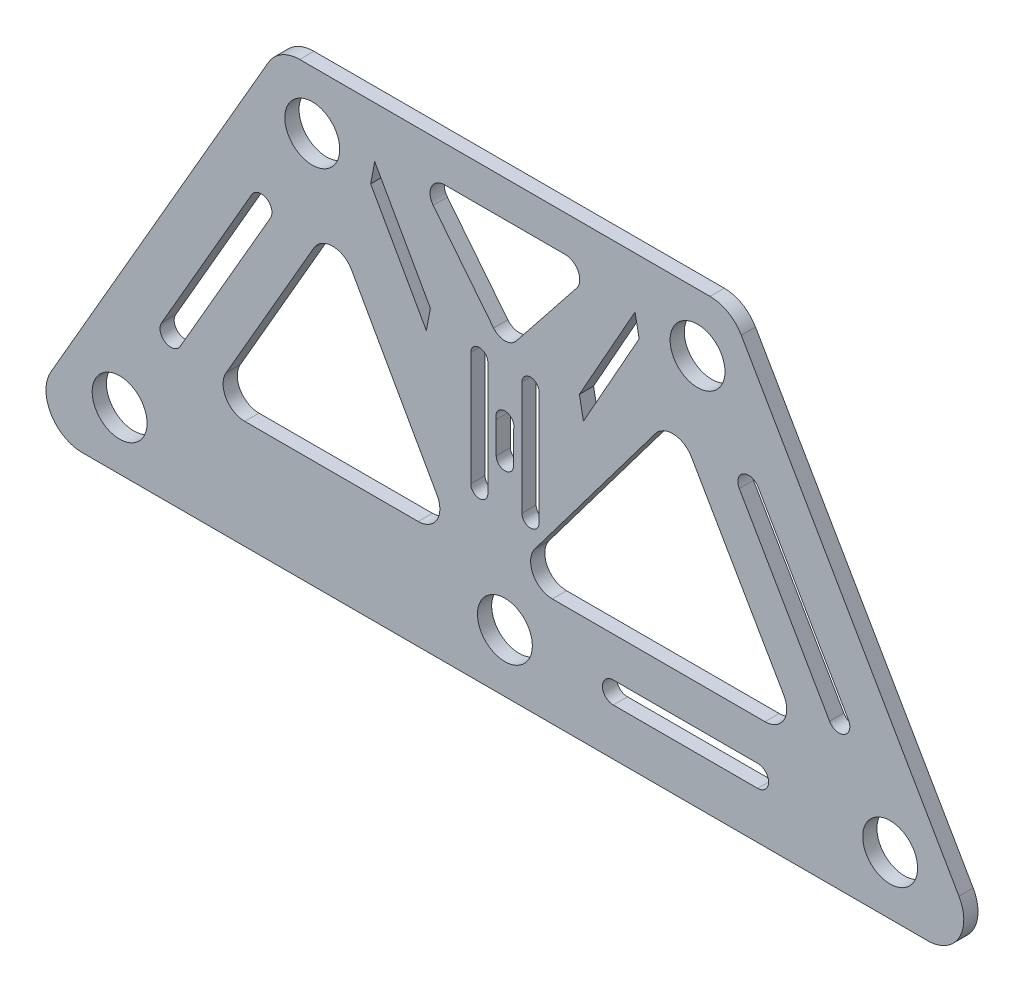
SolidWorks part; units mm, degrees
material "Acrylic (Medium-high impact)"
ref_plane "Front Plane" through (0, 0, 0) normal (0, 0, 1) x (1, 0, 0)
ref_plane "Top Plane" through (0, 0, 0) normal (0, 1, 0) x (1, 0, 0)
ref_plane "Right Plane" through (0, 0, 0) normal (1, 0, 0) x (0, 0, -1)
sketch "Sketch1" plane through (0, 0, 0) normal (0, 0, 1) x (1, 0, 0)
  line L0 (135.4667, 0) -> (-135.4667, 0) construction
  line L1 (0, 0) -> (135.4667, 0) construction
  line L4 (-135.4667, 0) -> (-67.7333, 117.3176) construction
  line L5 (0, 0) -> (0, 117.3176) construction
  line L6 (135.4667, 0) -> (67.7333, 117.3176) construction
  line L7 (-67.7333, 117.3176) -> (67.7333, 117.3176) construction
  line L8 (-72.1327, 137.6376) -> (72.1327, 137.6376)
  line L9 (159.6634, -1.27) -> (83.1313, 131.2876)
  line L10 (148.6649, -20.32) -> (-148.6649, -20.32)
  line L11 (-159.6634, -1.27) -> (-83.1313, 131.2876)
  line L12 (-79.4651, 137.6376) -> (79.4651, 137.6376) construction
  line L26 (170.6619, -20.32) -> (79.4651, 137.6376) construction
  line L27 (-170.6619, -20.32) -> (-79.4651, 137.6376) construction
  line L28 (170.6619, -20.32) -> (-170.6619, -20.32) construction
  circle A0 centre (0, 0) radius 9.65
  circle A1 centre (-135.4667, 0) radius 9.65
  circle A2 centre (135.4667, 0) radius 9.65
  circle A3 centre (-67.7333, 117.3176) radius 9.65
  circle A4 centre (135.4667, 0) radius 9.65
  circle A5 centre (67.7333, 117.3176) radius 9.65
  arc A6 (72.1327, 137.6376) -> (83.1313, 131.2876) centre (72.1327, 124.9376) cw
  arc A7 (-72.1327, 137.6376) -> (-83.1313, 131.2876) centre (-72.1327, 124.9376) ccw
  arc A8 (159.6634, -1.27) -> (148.6649, -20.32) centre (148.6649, -7.62) cw
  arc A9 (-148.6649, -20.32) -> (-159.6634, -1.27) centre (-148.6649, -7.62) cw
  dimension "D2" = 19.3
  dimension "D10" = 12.7
  dimension "D4" = 135.4667
  dimension "D5" = 20.32
  dimension "D8" = 135.4667
  dimension "D9" = 60
extrude "Boss-Extrude1" add sketch "Sketch1" along normal mid plane 5 contours A9 L10 A8 L9 A6 L8 A7 L11 A0 A1 A2 A3 A5
sketch "Sketch2" plane through (0, 0, 2.5) normal (0, 0, 1) x (1, 0, 0)
  line L4 (-8.7988, 12.7) -> (-60.401, 104.6176) construction
  line L5 (-113.4696, 12.7) -> (-8.7988, 12.7) construction
  line L6 (113.4696, 12.7) -> (-8.7988, 12.7) construction
  line L7 (60.401, 104.6176) -> (-8.7988, 12.7) construction
  line L8 (113.4696, 12.7) -> (60.401, 104.6176)
  line L9 (-113.4696, 12.7) -> (113.4696, 12.7)
  line L10 (-60.401, 104.6176) -> (-113.4696, 12.7)
  line L11 (60.401, 104.6176) -> (-60.401, 104.6176)
  line L12 (113.4696, 12.7) -> (60.401, 104.6176) construction
  line L13 (-17.4765, 17.78) -> (-60.4628, 94.3504)
  line L14 (-60.401, 104.6176) -> (-113.4696, 12.7) construction
  line L15 (60.401, 104.6176) -> (-60.401, 104.6176) construction
  line L16 (-60.4628, 94.3504) -> (-104.6708, 17.78)
  line L17 (-104.6708, 17.78) -> (-17.4765, 17.78)
  line L18 (59.841, 95.4275) -> (1.3843, 17.78)
  line L19 (104.6708, 17.78) -> (1.3843, 17.78)
  line L20 (104.6708, 17.78) -> (59.841, 95.4275)
  line L21 (-7.5568, 31.2422) -> (-43.0456, 94.4576) construction
  line L22 (40.0347, 94.4576) -> (-43.0456, 94.4576) construction
  line L23 (40.0347, 94.4576) -> (-7.5568, 31.2422) construction
  dimension "D2" = 104.6708
  dimension "D1" = 33.02
  dimension "D3" = 5.08
  dimension "D4" = 5.08
  dimension "D5" = 10.16
extrude "Cut-Extrude2" cut sketch "Sketch2" against normal through all
fillet "Fillet1" radius 7.62 6 edges at (104.6708, 17.78, 0) (59.841, 95.4275, 0) (1.3843, 17.78, 0) (-17.4765, 17.78, 0) (-60.4628, 94.3504, 0) (-104.6708, 17.78, 0)
sketch "Sketch3" plane through (0, 0, 2.5) normal (0, 0, 1) x (1, 0, 0)
  circle A0 centre (0, 63.5) radius 3.175
  dimension "D2" = 6.35
  dimension "D1" = 63.5
extrude "Cut-Extrude3" cut sketch "Sketch3" against normal blind 31.75
sketch "Sketch4" plane through (0, 0, 2.5) normal (0, 0, 1) x (1, 0, 0)
  line L32 (-114.1754, 29.2575) -> (-82.4254, 84.2501)
  line L33 (-89.0246, 88.0601) -> (-120.7746, 33.0675)
  line L34 (-47.2015, 112.2376) -> (-27.6203, 77.3581)
  line L35 (-26.1884, 84.8424) -> (-45.7696, 119.7218)
  line L36 (-45.7696, 119.7218) -> (-47.2015, 112.2376)
  line L37 (-27.6203, 77.3581) -> (-26.1884, 84.8424)
  line L38 (45.7696, 119.7218) -> (26.1884, 84.8424)
  line L39 (27.6203, 77.3581) -> (47.2015, 112.2376)
  line L40 (47.2015, 112.2376) -> (45.7696, 119.7218)
  line L41 (26.1884, 84.8424) -> (27.6203, 77.3581)
  line L42 (3.9789, 89.9504) -> (25.2109, 116.6993)
  line L43 (-25.2109, 116.6993) -> (-3.9789, 89.9504)
  line L44 (21.232, 124.9376) -> (-21.232, 124.9376)
  line L48 (82.4254, 84.2501) -> (114.1754, 29.2575)
  line L49 (120.7746, 33.0675) -> (89.0246, 88.0601)
  line L50 (88.9, 3.81) -> (38.1, 3.81)
  line L51 (38.1, -3.81) -> (88.9, -3.81)
  line L52 (-3.05, 63.5) -> (-3.05, 51.5)
  line L53 (3.05, 51.5) -> (3.05, 63.5)
  line L54 (6, 78.5) -> (6, 38.5)
  line L55 (12, 38.5) -> (12, 78.5)
  line L56 (-12, 78.5) -> (-12, 38.5)
  line L57 (-6, 38.5) -> (-6, 78.5)
  arc A26 (-120.7746, 33.0675) -> (-114.1754, 29.2575) centre (-117.475, 31.1625) ccw
  arc A27 (-82.4254, 84.2501) -> (-89.0246, 88.0601) centre (-85.725, 86.1551) ccw
  arc A28 (-3.9789, 89.9504) -> (3.9789, 89.9504) centre (0, 93.1086) ccw
  arc A29 (-21.232, 124.9376) -> (-25.2109, 116.6993) centre (-21.232, 119.8576) ccw
  arc A30 (25.2109, 116.6993) -> (21.232, 124.9376) centre (21.232, 119.8576) ccw
  arc A34 (114.1754, 29.2575) -> (120.7746, 33.0675) centre (117.475, 31.1625) ccw
  arc A35 (89.0246, 88.0601) -> (82.4254, 84.2501) centre (85.725, 86.1551) ccw
  arc A36 (38.1, 3.81) -> (38.1, -3.81) centre (38.1, 0) ccw
  arc A37 (88.9, -3.81) -> (88.9, 3.81) centre (88.9, 0) ccw
  arc A38 (3.05, 63.5) -> (-3.05, 63.5) centre (0, 63.5) ccw
  arc A39 (-3.05, 51.5) -> (3.05, 51.5) centre (0, 51.5) ccw
  arc A40 (12, 78.5) -> (6, 78.5) centre (9, 78.5) ccw
  arc A41 (6, 38.5) -> (12, 38.5) centre (9, 38.5) ccw
  arc A42 (-12, 38.5) -> (-6, 38.5) centre (-9, 38.5) ccw
  arc A43 (-6, 78.5) -> (-12, 78.5) centre (-9, 78.5) ccw
extrude "Cut-Extrude4" cut sketch "Sketch4" against normal through all
